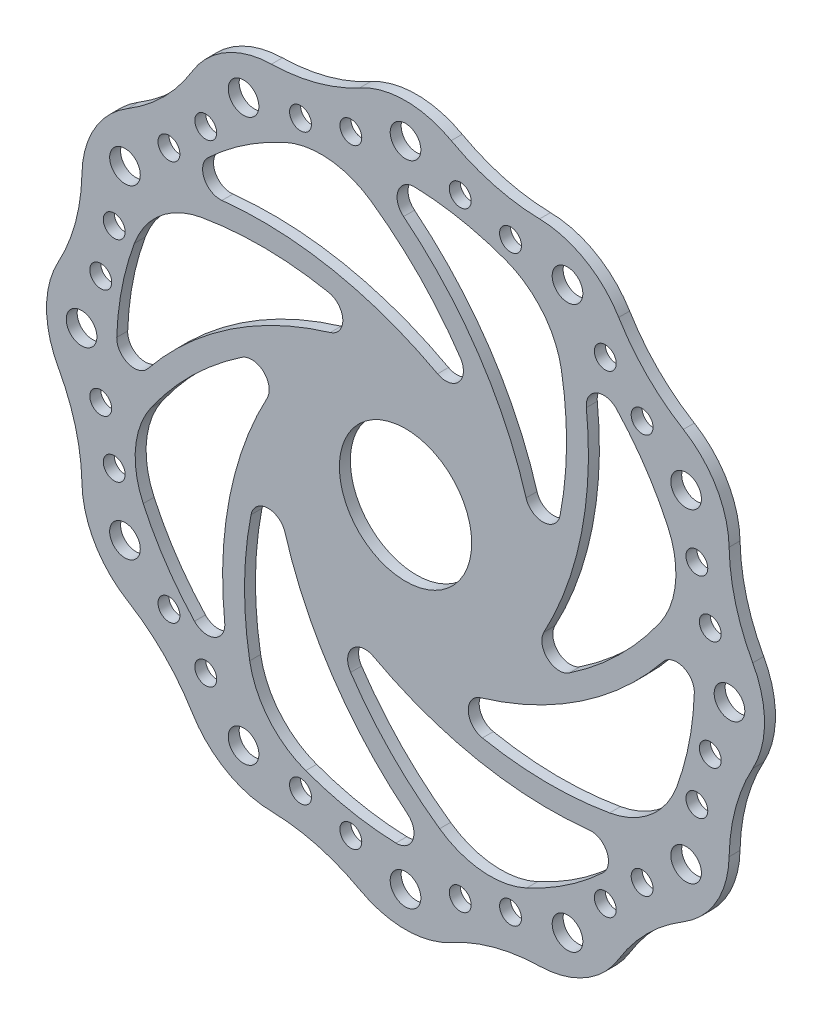
SolidWorks part; units mm, degrees
ref_plane "Front Plane" through (0, 0, 0) normal (0, 0, 1) x (1, 0, 0)
ref_plane "Top Plane" through (0, 0, 0) normal (0, 1, 0) x (1, 0, 0)
ref_plane "Right Plane" through (0, 0, 0) normal (1, 0, 0) x (0, 0, -1)
sketch "Sketch1" plane through (0, 0, 0) normal (0, 0, 1) x (1, 0, 0)
  arc A0 (3625.9097, 499.9535) -> (3623.2253, 510.3956) centre (3604.2581, 499.9535) ccw
  arc A1 (3619.299, 520.1541) -> (3623.2253, 510.3956) centre (3661.4806, 531.4566) ccw
  arc A2 (3617.82, 530.5682) -> (3614.9237, 540.9535) centre (3596.1729, 530.1278) ccw
  arc A3 (3617.82, 530.5682) -> (3619.299, 520.1541) centre (3661.4806, 531.4566) ccw
  arc A4 (3614.9237, 540.9535) -> (3607.3779, 548.6545) centre (3596.1729, 530.1278) ccw
  arc A5 (3599.0985, 555.1424) -> (3607.3779, 548.6545) centre (3629.9776, 586.0215) ccw
  arc A6 (3592.6106, 563.4218) -> (3584.9097, 570.9676) centre (3574.0839, 552.2168) ccw
  arc A7 (3592.6106, 563.4218) -> (3599.0985, 555.1424) centre (3629.9776, 586.0215) ccw
  arc A8 (3584.9097, 570.9676) -> (3574.5243, 573.8639) centre (3574.0839, 552.2168) ccw
  arc A9 (3564.1102, 575.3429) -> (3574.5243, 573.8639) centre (3575.4127, 617.5245) ccw
  arc A10 (3554.3518, 579.2691) -> (3543.9097, 581.9535) centre (3543.9097, 560.302) ccw
  arc A11 (3554.3518, 579.2691) -> (3564.1102, 575.3429) centre (3575.4127, 617.5245) ccw
  arc A12 (3543.9097, 581.9535) -> (3533.4676, 579.2691) centre (3543.9097, 560.302) ccw
  arc A13 (3523.7092, 575.3429) -> (3533.4676, 579.2691) centre (3512.4066, 617.5245) ccw
  arc A14 (3513.295, 573.8639) -> (3502.9097, 570.9676) centre (3513.7354, 552.2168) ccw
  arc A15 (3513.295, 573.8639) -> (3523.7092, 575.3429) centre (3512.4066, 617.5245) ccw
  arc A16 (3502.9097, 570.9676) -> (3495.2088, 563.4218) centre (3513.7354, 552.2168) ccw
  arc A17 (3488.7208, 555.1424) -> (3495.2088, 563.4218) centre (3457.8417, 586.0215) ccw
  arc A18 (3480.4414, 548.6545) -> (3472.8956, 540.9535) centre (3491.6464, 530.1278) ccw
  arc A19 (3480.4414, 548.6545) -> (3488.7208, 555.1424) centre (3457.8417, 586.0215) ccw
  arc A20 (3472.8956, 540.9535) -> (3469.9993, 530.5682) centre (3491.6464, 530.1278) ccw
  arc A21 (3468.5203, 520.1541) -> (3469.9993, 530.5682) centre (3426.3387, 531.4566) ccw
  arc A22 (3464.5941, 510.3956) -> (3461.9097, 499.9535) centre (3483.5612, 499.9535) ccw
  arc A23 (3464.5941, 510.3956) -> (3468.5203, 520.1541) centre (3426.3387, 531.4566) ccw
  arc A24 (3461.9097, 499.9535) -> (3464.5941, 489.5115) centre (3483.5612, 499.9535) ccw
  arc A25 (3468.5203, 479.753) -> (3464.5941, 489.5115) centre (3426.3387, 468.4505) ccw
  arc A26 (3469.9993, 469.3389) -> (3472.8956, 458.9535) centre (3491.6464, 469.7793) ccw
  arc A27 (3469.9993, 469.3389) -> (3468.5203, 479.753) centre (3426.3387, 468.4505) ccw
  arc A28 (3472.8956, 458.9535) -> (3480.4414, 451.2526) centre (3491.6464, 469.7793) ccw
  arc A29 (3488.7208, 444.7647) -> (3480.4414, 451.2526) centre (3457.8417, 413.8856) ccw
  arc A30 (3495.2088, 436.4853) -> (3502.9097, 428.9395) centre (3513.7354, 447.6903) ccw
  arc A31 (3495.2088, 436.4853) -> (3488.7208, 444.7647) centre (3457.8417, 413.8856) ccw
  arc A32 (3502.9097, 428.9395) -> (3513.295, 426.0432) centre (3513.7354, 447.6903) ccw
  arc A33 (3523.7092, 424.5642) -> (3513.295, 426.0432) centre (3512.4066, 382.3826) ccw
  arc A34 (3533.4676, 420.638) -> (3543.9097, 417.9535) centre (3543.9097, 439.6051) ccw
  arc A35 (3533.4676, 420.638) -> (3523.7092, 424.5642) centre (3512.4066, 382.3826) ccw
  arc A36 (3543.9097, 417.9535) -> (3554.3518, 420.638) centre (3543.9097, 439.6051) ccw
  arc A37 (3564.1102, 424.5642) -> (3554.3518, 420.638) centre (3575.4127, 382.3826) ccw
  arc A38 (3574.5243, 426.0432) -> (3584.9097, 428.9395) centre (3574.0839, 447.6903) ccw
  arc A39 (3574.5243, 426.0432) -> (3564.1102, 424.5642) centre (3575.4127, 382.3826) ccw
  arc A40 (3584.9097, 428.9395) -> (3592.6106, 436.4853) centre (3574.0839, 447.6903) ccw
  arc A41 (3599.0985, 444.7647) -> (3592.6106, 436.4853) centre (3629.9776, 413.8856) ccw
  arc A42 (3607.3779, 451.2526) -> (3614.9237, 458.9535) centre (3596.1729, 469.7793) ccw
  arc A43 (3607.3779, 451.2526) -> (3599.0985, 444.7647) centre (3629.9776, 413.8856) ccw
  arc A44 (3614.9237, 458.9535) -> (3617.82, 469.3389) centre (3596.1729, 469.7793) ccw
  arc A45 (3619.299, 479.753) -> (3617.82, 469.3389) centre (3661.4806, 468.4505) ccw
  arc A46 (3623.2253, 489.5115) -> (3625.9097, 499.9535) centre (3604.2581, 499.9535) ccw
  arc A47 (3623.2253, 489.5115) -> (3619.299, 479.753) centre (3661.4806, 468.4505) ccw
  circle A48 centre (3617.9097, 499.9535) radius 3.5
  circle A49 centre (3607.9955, 536.9535) radius 3.5
  circle A50 centre (3610.4474, 523.9394) radius 2.5
  circle A51 centre (3613.526, 512.45) radius 2.5
  circle A53 centre (3607.9955, 536.9535) radius 3.5
  circle A54 centre (3589.5401, 553.9948) radius 2.5
  circle A55 centre (3597.9509, 545.584) radius 2.5
  circle A56 centre (3580.9097, 564.0394) radius 3.5
  circle A57 centre (3556.4061, 569.5699) radius 2.5
  circle A58 centre (3567.8955, 566.4913) radius 2.5
  circle A59 centre (3543.9097, 573.9535) radius 3.5
  circle A60 centre (3519.9238, 566.4913) radius 2.5
  circle A61 centre (3531.4132, 569.5699) radius 2.5
  circle A62 centre (3506.9097, 564.0394) radius 3.5
  circle A63 centre (3489.8684, 545.584) radius 2.5
  circle A64 centre (3498.2792, 553.9948) radius 2.5
  circle A65 centre (3479.8238, 536.9535) radius 3.5
  circle A66 centre (3474.2934, 512.45) radius 2.5
  circle A67 centre (3477.3719, 523.9394) radius 2.5
  circle A68 centre (3469.9097, 499.9535) radius 3.5
  circle A69 centre (3477.3719, 475.9677) radius 2.5
  circle A70 centre (3474.2934, 487.4571) radius 2.5
  circle A71 centre (3479.8238, 462.9535) radius 3.5
  circle A72 centre (3498.2792, 445.9123) radius 2.5
  circle A73 centre (3489.8684, 454.3231) radius 2.5
  circle A74 centre (3506.9097, 435.8677) radius 3.5
  circle A75 centre (3531.4132, 430.3372) radius 2.5
  circle A76 centre (3519.9238, 433.4158) radius 2.5
  circle A77 centre (3543.9097, 425.9535) radius 3.5
  circle A78 centre (3567.8955, 433.4158) radius 2.5
  circle A79 centre (3556.4061, 430.3372) radius 2.5
  circle A80 centre (3580.9097, 435.8677) radius 3.5
  circle A81 centre (3597.9509, 454.3231) radius 2.5
  circle A82 centre (3589.5401, 445.9123) radius 2.5
  circle A83 centre (3607.9955, 462.9535) radius 3.5
  circle A84 centre (3613.526, 487.4571) radius 2.5
  circle A85 centre (3610.4474, 475.9677) radius 2.5
  arc A86 (3566.7139, 561.8887) -> (3546.1114, 565.9168) centre (3543.9097, 499.9535) ccw
  arc A87 (3571.4459, 517.1373) -> (3543.4674, 558.805) centre (3490.3336, 492.9001) ccw
  arc A88 (3579.2037, 517.5123) -> (3579.5049, 546.5637) centre (3501.0381, 532.85) ccw
  arc A89 (3579.5049, 546.5637) -> (3566.7139, 561.8887) centre (3559.8035, 543.1205) ccw
  arc A90 (3546.1114, 565.9168) -> (3543.4674, 558.805) centre (3545.9779, 561.919) ccw
  arc A91 (3571.4459, 517.1373) -> (3579.2037, 517.5123) centre (3575.2785, 518.2825) ccw
  arc A92 (3516.2399, 559.8733) -> (3498.8234, 548.1535) centre (3543.9097, 499.9535) ccw
  arc A93 (3551.23, 531.5754) -> (3501.9826, 541.2551) centre (3511.0132, 457.082) ccw
  arc A94 (3551.23, 531.5754) -> (3556.4504, 537.3261) centre (3553.1303, 535.0952) ccw
  arc A95 (3498.8234, 548.1535) -> (3501.9826, 541.2551) centre (3501.5559, 545.2323) ccw
  arc A96 (3556.4504, 537.3261) -> (3536.1209, 558.0815) centre (3490.3336, 492.9001) ccw
  arc A97 (3536.1209, 558.0815) -> (3516.2399, 559.8733) centre (3524.6247, 541.7158) ccw
  arc A98 (3481.9745, 522.7577) -> (3477.9464, 502.1553) centre (3543.9097, 499.9535) ccw
  arc A99 (3526.7259, 527.4898) -> (3485.0582, 499.5113) centre (3550.9631, 446.3775) ccw
  arc A100 (3526.7259, 527.4898) -> (3526.3509, 535.2475) centre (3525.5807, 531.3224) ccw
  arc A101 (3477.9464, 502.1553) -> (3485.0582, 499.5113) centre (3481.9442, 502.0218) ccw
  arc A102 (3526.3509, 535.2475) -> (3497.2995, 535.5488) centre (3511.0132, 457.082) ccw
  arc A103 (3497.2995, 535.5488) -> (3481.9745, 522.7577) centre (3500.7427, 515.8474) ccw
  arc A104 (3483.9899, 472.2838) -> (3495.7097, 454.8673) centre (3543.9097, 499.9535) ccw
  arc A105 (3512.2878, 507.2739) -> (3502.6081, 458.0265) centre (3586.7812, 467.0571) ccw
  arc A106 (3512.2878, 507.2739) -> (3506.5371, 512.4943) centre (3508.768, 509.1741) ccw
  arc A107 (3495.7097, 454.8673) -> (3502.6081, 458.0265) centre (3498.631, 457.5998) ccw
  arc A108 (3506.5371, 512.4943) -> (3485.7817, 492.1648) centre (3550.9631, 446.3775) ccw
  arc A109 (3485.7817, 492.1648) -> (3483.9899, 472.2838) centre (3502.1474, 480.6685) ccw
  arc A110 (3521.1055, 438.0184) -> (3541.708, 433.9903) centre (3543.9097, 499.9535) ccw
  arc A111 (3516.3734, 482.7698) -> (3544.352, 441.1021) centre (3597.4857, 507.007) ccw
  arc A112 (3516.3734, 482.7698) -> (3508.6157, 482.3948) centre (3512.5408, 481.6246) ccw
  arc A113 (3541.708, 433.9903) -> (3544.352, 441.1021) centre (3541.8414, 437.9881) ccw
  arc A114 (3508.6157, 482.3948) -> (3508.3145, 453.3434) centre (3586.7812, 467.0571) ccw
  arc A115 (3508.3145, 453.3434) -> (3521.1055, 438.0184) centre (3528.0158, 456.7866) ccw
  arc A116 (3571.5795, 440.0338) -> (3588.9959, 451.7536) centre (3543.9097, 499.9535) ccw
  arc A117 (3536.5893, 468.3317) -> (3585.8367, 458.652) centre (3576.8062, 542.8251) ccw
  arc A118 (3536.5893, 468.3317) -> (3531.369, 462.581) centre (3534.6891, 464.8119) ccw
  arc A119 (3588.9959, 451.7536) -> (3585.8367, 458.652) centre (3586.2634, 454.6748) ccw
  arc A120 (3531.369, 462.581) -> (3551.6984, 441.8256) centre (3597.4857, 507.007) ccw
  arc A121 (3551.6984, 441.8256) -> (3571.5795, 440.0338) centre (3563.1947, 458.1913) ccw
  arc A122 (3605.8449, 477.1494) -> (3609.8729, 497.7518) centre (3543.9097, 499.9535) ccw
  arc A123 (3561.0934, 472.4173) -> (3602.7612, 500.3958) centre (3536.8562, 553.5296) ccw
  arc A124 (3561.0934, 472.4173) -> (3561.4684, 464.6596) centre (3562.2386, 468.5847) ccw
  arc A125 (3609.8729, 497.7518) -> (3602.7612, 500.3958) centre (3605.8752, 497.8853) ccw
  arc A126 (3561.4684, 464.6596) -> (3590.5198, 464.3583) centre (3576.8062, 542.8251) ccw
  arc A127 (3590.5198, 464.3583) -> (3605.8449, 477.1494) centre (3587.0766, 484.0597) ccw
  arc A128 (3603.8295, 527.6233) -> (3592.1096, 545.0398) centre (3543.9097, 499.9535) ccw
  arc A129 (3575.5315, 492.6332) -> (3585.2112, 541.8806) centre (3501.0381, 532.85) ccw
  arc A130 (3575.5315, 492.6332) -> (3581.2822, 487.4128) centre (3579.0513, 490.733) ccw
  arc A131 (3592.1096, 545.0398) -> (3585.2112, 541.8806) centre (3589.1884, 542.3073) ccw
  arc A132 (3581.2822, 487.4128) -> (3602.0377, 507.7423) centre (3536.8562, 553.5296) ccw
  arc A133 (3602.0377, 507.7423) -> (3603.8295, 527.6233) centre (3585.6719, 519.2386) ccw
extrude "Boss-Extrude1" add sketch "Sketch1" along normal blind 2.5
sketch "Sketch2" plane through (0, 0, 0) normal (0, 0, -1) x (-1, 0, 0)
  line L0 (-3543.9097, 594.7908) -> (-3543.9097, 409.1527) construction
  line L1 (-3543.9097, 501.9718) -> (-3432.748, 501.9718) construction
  line L2 (-3432.748, 501.9718) -> (-3644.0986, 501.9718) construction
  circle A0 centre (-3543.9097, 501.9718) radius 15.1092
extrude "Cut-Extrude1" cut sketch "Sketch2" along normal mid plane 10
